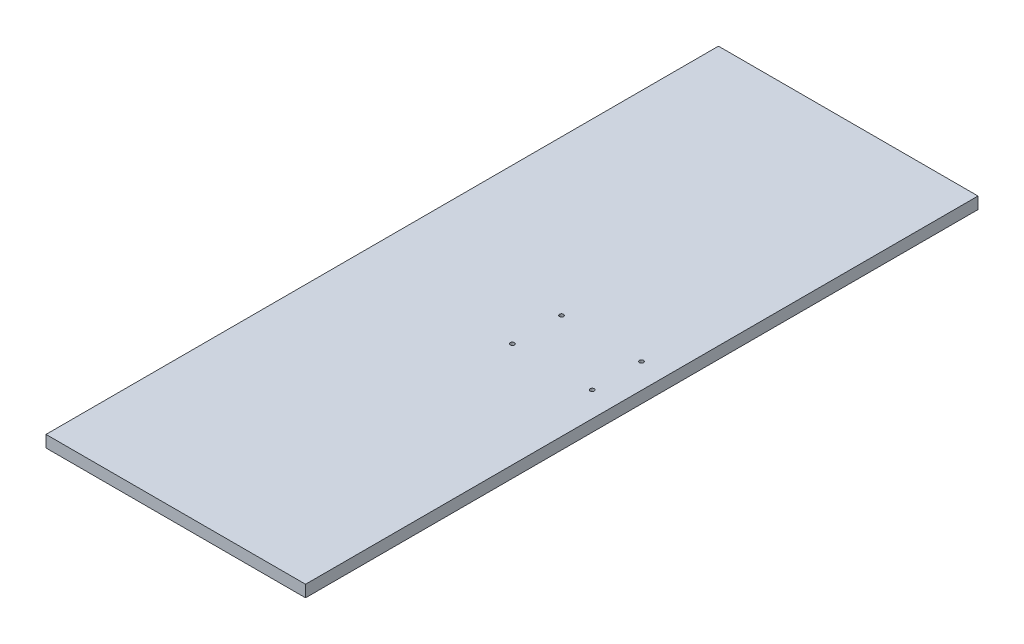
SolidWorks part; units mm, degrees
ref_plane "Front Plane" through (0, 0, 0) normal (0, 0, 1) x (1, 0, 0)
ref_plane "Top Plane" through (0, 0, 0) normal (0, 1, 0) x (1, 0, 0)
ref_plane "Right Plane" through (0, 0, 0) normal (1, 0, 0) x (0, 0, -1)
sketch "Sketch1" plane through (0, 0, 0) normal (0, 1, 0) x (1, 0, 0)
  line L1 (110, -285) -> (-110, -285)
  line L2 (110, -285) -> (110, 285)
  line L3 (110, 285) -> (-110, 285)
  line L4 (-110, -285) -> (-110, 285)
  line L5 (110, -285) -> (-110, 285) construction
  line L6 (110, 285) -> (-110, -285) construction
  point P0 (0, 0)
  dimension "D1" = 220
  dimension "D2" = 570
extrude "Boss-Extrude1" add sketch "Sketch1" along normal blind 10
sketch "Sketch2" plane through (0, 10, 0) normal (0, 1, 0) x (1, 0, 0)
  line L0 (21.16, 20.84) -> (21.16, -20.84) construction
  line L1 (21.16, -20.84) -> (88.84, -20.84) construction
  line L2 (88.84, -20.84) -> (88.84, 20.84) construction
  line L3 (88.84, 20.84) -> (21.16, 20.84) construction
  line L4 (110, -285) -> (110, 285) construction
  circle A0 centre (21.16, 20.84) radius 1.75
  circle A1 centre (88.84, 20.84) radius 1.75
  circle A2 centre (21.16, -20.84) radius 1.75
  circle A3 centre (88.84, -20.84) radius 1.75
  point P8 (88.84, 0)
  dimension "D1" = 3.5
  dimension "D2" = 41.68
  dimension "D3" = 67.68
  dimension "D4" = 21.16
extrude "Cut-Extrude1" cut sketch "Sketch2" against normal blind 10
